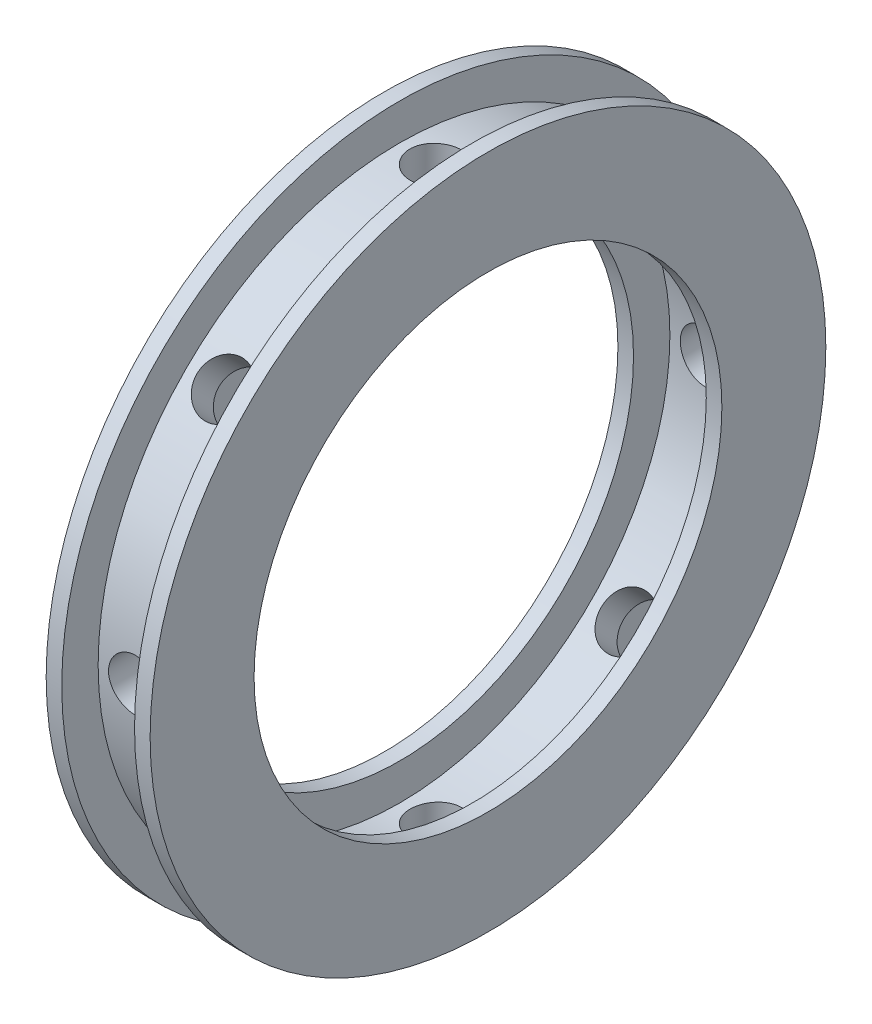
SolidWorks part; units mm, degrees
ref_plane "Front Plane" through (0, 0, 0) normal (0, 0, 1) x (1, 0, 0)
ref_plane "Top Plane" through (0, 0, 0) normal (0, 1, 0) x (1, 0, 0)
ref_plane "Right Plane" through (0, 0, 0) normal (1, 0, 0) x (0, 0, -1)
sketch "Sketch1" plane through (0, 0, 0) normal (0, 0, 1) x (1, 0, 0)
  line L0 (0, 0) -> (0, 29) construction
  line L1 (-5.6086, 0) -> (5.6086, 0) construction
  line L2 (-3.5, 29) -> (3.5, 29)
  line L3 (3.5, 29) -> (3.5, 32.5)
  line L4 (3.5, 32.5) -> (5, 32.5)
  line L5 (5, 32.5) -> (5, 22.5)
  line L6 (5, 22.5) -> (3.5, 22.5)
  line L7 (3.5, 22.5) -> (3.5, 26)
  line L8 (3.5, 26) -> (-3.5, 26)
  line L9 (-3.5, 22.5) -> (-3.5, 26)
  line L10 (-5, 22.5) -> (-3.5, 22.5)
  line L11 (-5, 32.5) -> (-5, 22.5)
  line L12 (-3.5, 32.5) -> (-5, 32.5)
  line L13 (-3.5, 29) -> (-3.5, 32.5)
  point P6 (0, 0)
  point P14 (0, 26)
  dimension "D1" = 1.5
  dimension "D2" = 7
  dimension "D3" = 45
  dimension "D4" = 52
  dimension "D5" = 58
  dimension "D6" = 65
revolve "Revolve1" add sketch "Sketch1" angle 360 about L1
sketch "Sketch2" plane through (0, 0, 0) normal (0, 1, 0) x (1, 0, 0)
  circle A0 centre (0, 0) radius 2.5
  dimension "D1" = 5
extrude "Cut-Extrude1" cut sketch "Sketch2" along normal through all
pattern_circular "CirPattern1" count 8 over 360 about axis through (-5.6086, 0, 0) along (-1, 0, 0) of "Cut-Extrude1"
